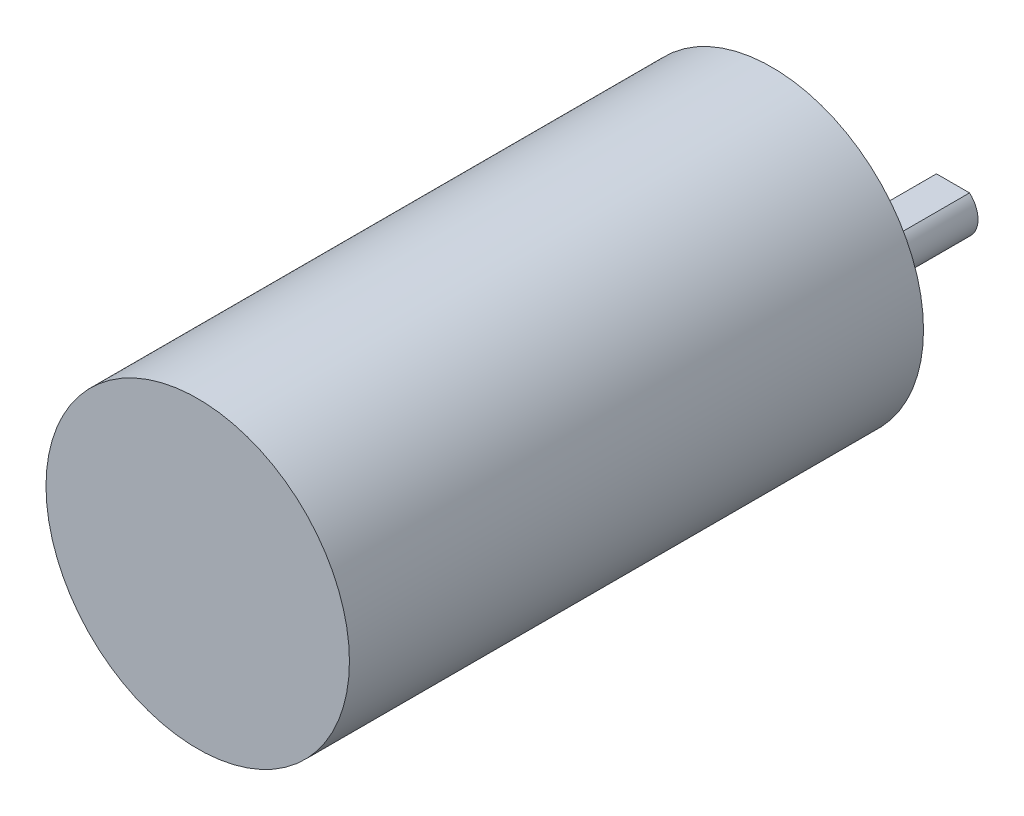
SolidWorks part; units mm, degrees
other "Markup1"
sketch "Sketch6" plane through (-18.5, -18.5, -22.098) normal (-0.4295, -0.0043, -0.903) x (-0.9028, -0.0222, 0.4295)
ref_plane "Front Plane" through (0, 0, 0) normal (0, 0, 1) x (1, 0, 0)
ref_plane "Top Plane" through (0, 0, 0) normal (0, 1, 0) x (1, 0, 0)
ref_plane "Right Plane" through (0, 0, 0) normal (1, 0, 0) x (0, 0, -1)
sketch "Sketch1" plane through (0, 0, 0) normal (0, 0, 1) x (1, 0, 0)
  circle A0 centre (0, 0) radius 18.5
  dimension "D1" = 37
extrude "Boss-Extrude1" add sketch "Sketch1" along normal blind 70
sketch "Sketch2" plane through (0, 0, 0) normal (0, 0, -1) x (-1, 0, 0)
  circle A0 centre (0, -7.112) radius 5.969
  dimension "D2" = 11.938
  dimension "D1" = 7.112
extrude "Boss-Extrude2" add sketch "Sketch2" along normal blind 6.096
sketch "Sketch3" plane through (0, 0, -6.096) normal (0, 0, -1) x (-1, 0, 0)
  circle A0 centre (0, -7.112) radius 3.048
  dimension "D1" = 6.096
extrude "Boss-Extrude3" add sketch "Sketch3" along normal blind 16.002
sketch "Sketch4" plane through (0, 0, 0) normal (0, 0, -1) x (-1, 0, 0)
  line L6 (-15.2766, 0) -> (-7.7942, 13.2141) construction
  line L7 (7.7942, 13.2141) -> (15.2766, 0) construction
  line L8 (-15.2766, 0) -> (15.2766, 0) construction
  line L9 (-15.2766, 0) -> (-7.7942, -13.5675) construction
  line L10 (7.7942, -13.5675) -> (15.2766, 0) construction
  line L11 (-16.8766, 0) -> (-18.5, 0) construction
  line L12 (-7.7942, 13.2141) -> (-8.9086, 16.2138) construction
  circle A0 centre (-15.2766, 0) radius 1.6
  circle A1 centre (15.2766, 0) radius 1.6
  circle A2 centre (7.7942, -13.5675) radius 1.6
  circle A3 centre (-7.7942, -13.5675) radius 1.6
  circle A4 centre (-7.7942, 13.2141) radius 1.6
  circle A5 centre (7.7942, 13.2141) radius 1.6
  circle A7 centre (0, 0) radius 18.5 construction
  point P12 (0, 0)
  point P18 (-8.3514, 14.714)
  dimension "D1" = 1.6234
  dimension "D4" = 3.2
  dimension "D2" = 30.988
  dimension "D3" = 15.494
  dimension "D5" = 2.9997
extrude "Cut-Extrude1" cut sketch "Sketch4" against normal blind 3
sketch "Sketch5" plane through (0, 0, -22.098) normal (0, 0, -1) x (-1, 0, 0)
  line L1 (-2.0161, -4.826) -> (2.0161, -4.826)
  line L2 (-2.0161, -4.826) -> (-2.0161, -4.064)
  line L3 (-2.0161, -4.064) -> (2.0161, -4.064)
  line L4 (2.0161, -4.826) -> (2.0161, -4.064)
  circle A0 centre (0, -7.112) radius 3.048 construction
  dimension "D1" = 0.762
extrude "Cut-Extrude2" cut sketch "Sketch5" against normal up to surface (16.002 mm away) up to face at (-3.048, -7.112, -6.096)
